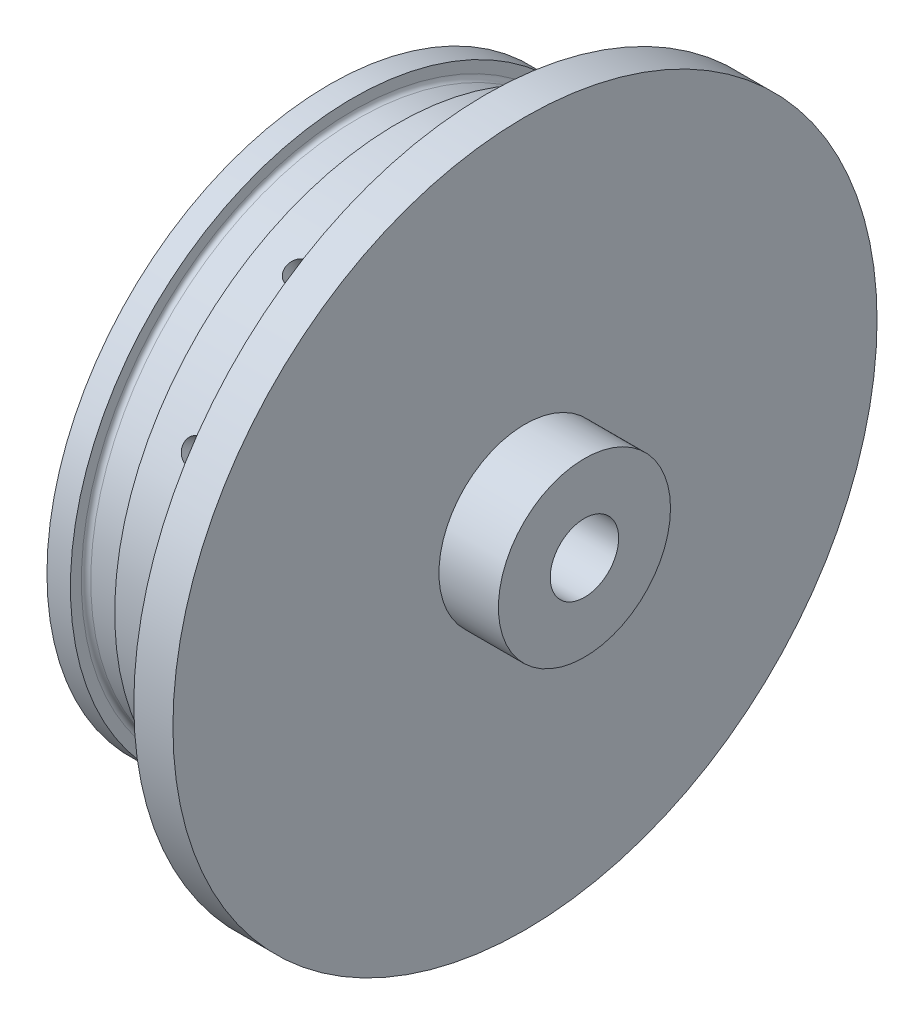
SolidWorks part; units mm, degrees
material "6061-T6 (SS)"
ref_plane "Front Plane" through (0, 0, 0) normal (0, 0, 1) x (1, 0, 0)
ref_plane "Top Plane" through (0, 0, 0) normal (0, 1, 0) x (1, 0, 0)
ref_plane "Right Plane" through (0, 0, 0) normal (1, 0, 0) x (0, 0, -1)
sketch "Sketch1" plane through (0, 0, 0) normal (1, 0, 0) x (0, 0, -1)
  circle A0 centre (0, 0) radius 57.15
  dimension "D1" = 114.3
extrude "Boss-Extrude1" add sketch "Sketch1" along normal blind 6.35
sketch "Sketch2" plane through (0, 0, 0) normal (-1, 0, 0) x (0, 0, 1)
  circle A0 centre (0, 0) radius 45.847
  dimension "D1" = 91.694
extrude "Boss-Extrude2" add sketch "Sketch2" along normal blind 25.4
sketch "Sketch10" plane through (0, 0, 0) normal (0, 1, 0) x (1, 0, 0)
  line L0 (0, 0) -> (-53.2238, 0) construction
  line L1 (-26.2636, 0) -> (26.2636, 0) construction
  line L2 (0, 0) -> (0, 64.5447) construction
  line L3 (0, -62.865) -> (0, 62.865) construction
ref_plane "Plane1" through (0, 0, -45.847) normal (0, 0, -1) x (-1, 0, 0)
sketch "Sketch11" plane through (0, 0, -45.847) normal (0, 0, -1) x (-1, 0, 0)
  line L0 (0, 0) -> (53.2238, 0) construction
  line L1 (0, -45.847) -> (0, 45.847) construction
  circle A0 centre (7.62, 0) radius 1.8986
  dimension "D2" = 3.7973
  dimension "D1" = 7.62
extrude "Cut-Extrude3" cut sketch "Sketch11" against normal blind 10.16
pattern_circular "CirPattern1" count 12 over 360 about axis through (0, 0, 0) along (1, 0, 0) of "Cut-Extrude3"
sketch "Sketch15" plane through (6.35, 0, 0) normal (1, 0, 0) x (0, 0, -1)
  circle A0 centre (0, 0) radius 5.5562
  dimension "D1" = 11.1125
extrude "Cut-Extrude4" cut sketch "Sketch15" against normal through all both and the other way through all
sketch "Sketch16" plane through (0, 0, 0) normal (0, 0, 1) x (1, 0, 0)
  line L0 (-9.5186, 45.847) -> (-25.4, 45.847) construction
  line L1 (-21.59, 45.847) -> (-14.4018, 45.847)
  line L2 (-21.59, 45.847) -> (-21.59, 44.069)
  line L3 (-20.828, 43.307) -> (-15.1638, 43.307)
  line L4 (-14.4018, 45.847) -> (-14.4018, 44.069)
  line L5 (0, 0) -> (-53.2238, 0) construction
  line L6 (-25.4, 45.847) -> (-25.4, -45.847) construction
  arc A0 (-14.4018, 44.069) -> (-15.1638, 43.307) centre (-15.1638, 44.069) cw
  arc A1 (-20.828, 43.307) -> (-21.59, 44.069) centre (-20.828, 44.069) cw
  point P8 (-26.6119, 0)
  point P13 (-14.4018, 43.307)
  point P16 (-21.59, 43.307)
  dimension "D4" = 0.762
  dimension "D1" = 43.307
  dimension "D2" = 3.81
  dimension "D3" = 7.1882
revolve "Cut-Revolve1" cut sketch "Sketch16" angle 360 about L0
sketch "Sketch17" plane through (6.35, 0, 0) normal (1, 0, 0) x (0, 0, -1)
  circle A0 centre (0, 0) radius 13.97
  circle A1 centre (0, 0) radius 5.5562
  dimension "D1" = 27.94
  dimension "D2" = 11.1125
extrude "Boss-Extrude3" add sketch "Sketch17" along normal blind 9.652
cosmetic thread "Cosmetic Thread1" parameters "D2"=23.1953
sketch "Sketch18" plane through (-25.4, 0, 0) normal (-1, 0, 0) x (0, 0, 1)
  circle A0 centre (0, 0) radius 38.354
  dimension "D1" = 76.708
extrude "Cut-Extrude5" cut sketch "Sketch18" against normal blind 6.604
sketch "Sketch19" plane through (-18.796, 0, 0) normal (-1, 0, 0) x (0, 0, 1)
  line L0 (0, 0) -> (0, 57.15) construction
  circle A0 centre (0, 0) radius 57.15 construction
  circle A1 centre (0, 33.3375) radius 1.1303
  circle A2 centre (23.5732, 23.5732) radius 1.1303
  circle A3 centre (33.3375, 0) radius 1.1303
  circle A4 centre (23.5732, -23.5732) radius 1.1303
  circle A5 centre (0, -33.3375) radius 1.1303
  circle A6 centre (-23.5732, -23.5732) radius 1.1303
  circle A7 centre (-33.3375, 0) radius 1.1303
  circle A8 centre (-23.5732, 23.5732) radius 1.1303
  point P24 (0, 0)
  dimension "D2" = 2.2606
  dimension "D1" = 33.3375
  dimension "D3" = 8
extrude "Cut-Extrude6" cut sketch "Sketch19" against normal blind 6.35
sketch "Sketch20" plane through (0, 0, 0) normal (0, 0, 1) x (1, 0, 0)
  line L0 (0, 0) -> (-18.796, 0)
  line L1 (-18.796, 27.94) -> (0, 15.875)
  line L3 (-18.796, 27.94) -> (-18.796, 0)
  line L4 (0, 45.847) -> (0, -45.847) construction
  line L5 (0, 15.875) -> (0, 0)
  dimension "D1" = 27.94
  dimension "D2" = 18.796
  dimension "D3" = 15.875
revolve "Cut-Revolve2" cut sketch "Sketch20" angle 360 about L0
